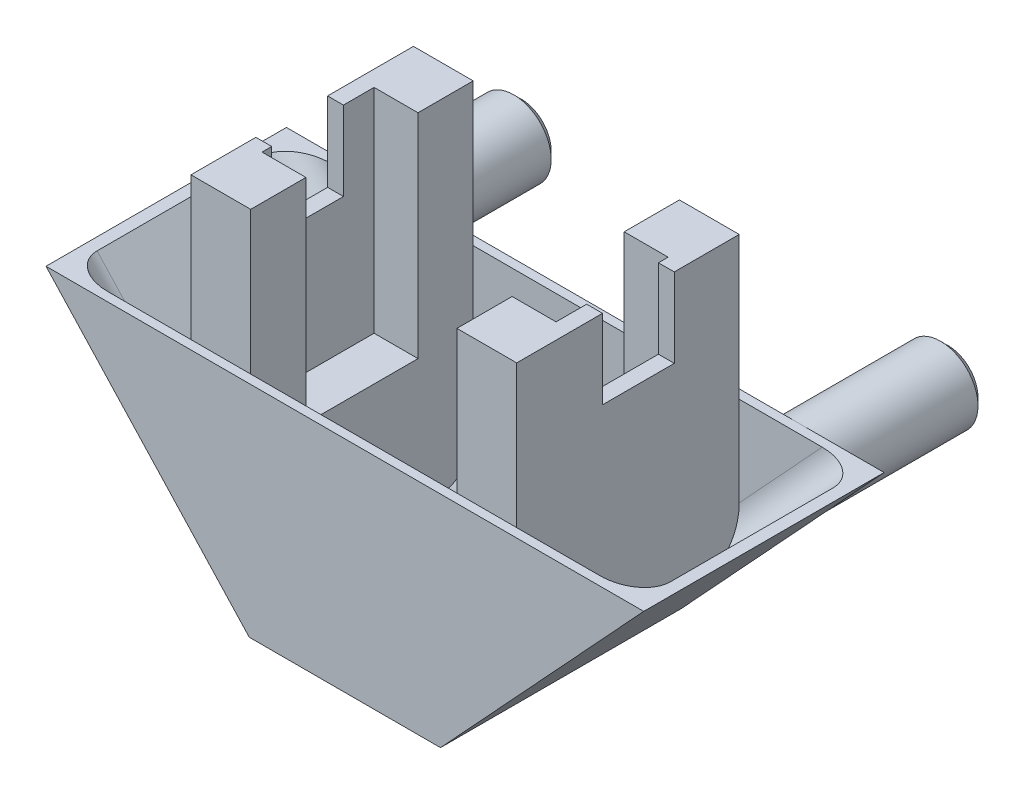
SolidWorks part; units mm, degrees
ref_plane "Ebene vorne" through (0, 0, 0) normal (0, 0, 1) x (1, 0, 0)
ref_plane "Ebene oben" through (0, 0, 0) normal (0, 1, 0) x (1, 0, 0)
ref_plane "Ebene rechts" through (0, 0, 0) normal (1, 0, 0) x (0, 0, -1)
sketch "Skizze4" plane through (0, 0, 0) normal (0, 0, 1) x (1, 0, 0)
  line L0 (-6.4, 0) -> (-20, 14.7)
  line L1 (-20, 14.7) -> (20, 14.7)
  line L2 (20, 14.7) -> (6.4, 0)
  line L3 (6.4, 0) -> (-6.4, 0)
  dimension "D1" = 12.8
  dimension "D2" = 40
  dimension "D3" = 14.7
extrude "Aufsatz-Linear austragen1" add sketch "Skizze4" along normal blind 16.09
shell "Wandung2" thickness 0.6
fillet "Verrundung1" radius 2 2 edges at (12.3826, 7.35, 15.49) (-12.3826, 7.35, 15.49)
fillet "Verrundung2" radius 2 2 edges at (12.3826, 7.35, 0.6) (-12.3826, 7.35, 0.6)
ref_plane "Ebene1" through (20, 0, 0) normal (1, 0, 0) x (0, 0, -1)
sketch "Skizze7" plane through (0, 0, 0) normal (0, 0, -1) x (-1, 0, 0)
  line L0 (-6.4, 0) -> (-20, 14.7) construction
  line L1 (-20, 14.7) -> (20, 14.7) construction
  line L2 (20, 14.7) -> (6.4, 0) construction
  circle A0 centre (-14.2813, 12.2) radius 2.5
  circle A1 centre (14.2813, 12.2) radius 2.5
  dimension "D1" = 5
extrude "Aufsatz-Linear austragen4" add sketch "Skizze7" along normal blind 10
chamfer "Fase3" distance 0.5 angle 45 2 edges at (11.7813, 12.2, -10) (-16.7813, 12.2, -10)
ref_plane "Ebene2" through (0, 4, 0) normal (0, 1, 0) x (1, 0, 0)
ref_plane "Ebene4" through (0, 0, 8.045) normal (0, 0, 1) x (1, 0, 0)
sketch "Skizze12" plane through (0, 0, 8.045) normal (0, 0, 1) x (1, 0, 0)
  line L0 (6.9, 0.5404) -> (6.9, 10)
  line L1 (6.4, 0) -> (20, 14.7) construction
  line L2 (6.9, 10) -> (10.9, 10)
  line L5 (-6.4, 0) -> (6.4, 0) construction
  line L6 (10.9, 10) -> (10.9, 4.864)
  line L7 (10.9, 4.864) -> (6.9, 0.5404)
  dimension "D1" = 0.5
  dimension "D2" = 10
  dimension "D3" = 4
extrude "Aufsatz-Linear austragen8" add sketch "Skizze12" along normal mid plane 15.7
ref_plane "Ebene5" through (9.84, 0, 0) normal (-1, 0, 0) x (0, 0, 1)
ref_plane "Ebene3" through (0, 0, 8.045) normal (0, 0, 1) x (1, 0, 0)
mirror "Spiegeln6" about plane through (0, 0, 0) normal (1, 0, 0) of "Aufsatz-Linear austragen8"
sketch "Skizze14" plane through (9.84, 0, 0) normal (-1, 0, 0) x (0, 0, 1)
  line L0 (15.49, 10) -> (0.6, 10) construction
  line L1 (4.295, 10) -> (0.6, 10)
  line L2 (4.295, 10) -> (4.295, 24.25)
  line L3 (4.295, 24.25) -> (0.6, 24.25)
  line L4 (0.6, 10) -> (0.6, 24.25)
  line L5 (15.49, 14.7) -> (15.49, 8.6925) construction
  line L6 (11.795, 10) -> (15.49, 10)
  line L7 (11.795, 10) -> (11.795, 24.25)
  line L8 (11.795, 24.25) -> (15.49, 24.25)
  line L9 (15.49, 10) -> (15.49, 24.25)
  line L10 (0.6, 10) -> (0.6, 4.369) construction
  point P10 (15.49, 10)
  point P13 (0.6, 10)
  point P16 (0.6, 21.9251)
  dimension "D1" = 7.5
  dimension "D2" = 14.25
extrude "Aufsatz-Linear austragen9" add sketch "Skizze14" along normal up to vertex
sketch "Skizze15" plane through (9.84, 0, 0) normal (1, 0, 0) x (0, 0, -1)
  line L0 (-15.49, 14.7) -> (-15.49, 24.25) construction
  line L1 (-0.6, 24.25) -> (-15.49, 24.25)
  line L2 (-0.6, 24.25) -> (-0.6, 9.73)
  line L3 (-0.6, 9.73) -> (-15.49, 9.73)
  line L4 (-15.49, 24.25) -> (-15.49, 9.73)
  point P4 (-15.49, 24.25)
  dimension "D1" = 14.52
extrude "Aufsatz-Linear austragen10" add sketch "Skizze15" along normal up to vertex (1.06 mm away)
sketch "Skizze16" plane through (9.84, 0, 0) normal (-1, 0, 0) x (0, 0, 1)
  line L0 (4.295, 24.25) -> (11.795, 24.25) construction
  line L1 (4.945, 24.25) -> (9.745, 24.25)
  line L2 (4.945, 24.25) -> (4.945, 18.95)
  line L3 (4.945, 18.95) -> (9.745, 18.95)
  line L4 (9.745, 24.25) -> (9.745, 18.95)
  line L5 (4.295, 10) -> (4.295, 24.25) construction
  dimension "D1" = 0.65
  dimension "D2" = 5.3
  dimension "D3" = 4.8
extrude "Schnitt-Linear austragen1" cut sketch "Skizze16" against normal up to next
mirror "Spiegeln9" about plane through (0, 0, 0) normal (1, 0, 0) of "Aufsatz-Linear austragen9"
sketch "Skizze17" plane through (-9.84, 0, 0) normal (-1, 0, 0) x (0, 0, 1)
  line L1 (15.49, 9.73) -> (0.6, 9.73)
  line L2 (15.49, 9.73) -> (15.49, 24.25)
  line L3 (15.49, 24.25) -> (0.6, 24.25)
  line L4 (0.6, 9.73) -> (0.6, 24.25)
  dimension "D1" = 14.52
extrude "Aufsatz-Linear austragen11" add sketch "Skizze17" along normal up to vertex (1.06 mm away)
sketch "Skizze18" plane through (-9.84, 0, 0) normal (1, 0, 0) x (0, 0, -1)
  line L0 (-11.145, 24.25) -> (-11.145, 18.95)
  line L1 (-9.745, 24.25) -> (-15.49, 24.25) construction
  line L2 (-11.145, 18.95) -> (-6.345, 18.95)
  line L3 (-9.745, 18.95) -> (-4.945, 18.95) construction
  line L4 (-6.345, 18.95) -> (-6.345, 24.25)
  line L5 (-11.795, 24.25) -> (-4.295, 24.25) construction
  line L6 (-6.345, 24.25) -> (-11.145, 24.25)
  line L7 (-11.795, 24.25) -> (-11.795, 10) construction
  dimension "D1" = 5.3
  dimension "D2" = 4.8
  dimension "D3" = 0.65
extrude "Schnitt-Linear austragen2" cut sketch "Skizze18" against normal up to next
